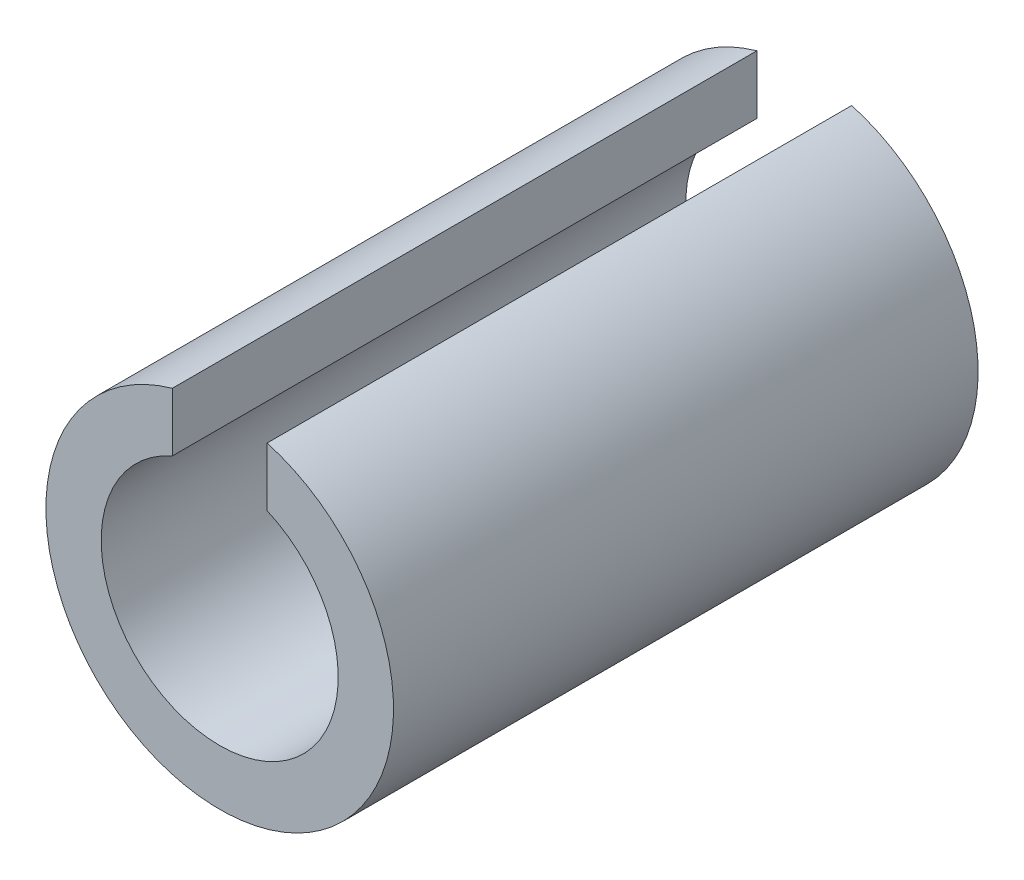
SolidWorks part; units mm, degrees
material "AISI 1020"
ref_plane "Спереди" through (0, 0, 0) normal (0, 0, 1) x (1, 0, 0)
ref_plane "Сверху" through (0, 0, 0) normal (0, 1, 0) x (1, 0, 0)
ref_plane "Справа" through (0, 0, 0) normal (1, 0, 0) x (0, 0, -1)
sketch "Эскиз1" plane through (0, 0, 0) normal (0, 0, 1) x (1, 0, 0)
  line L0 (3, 4.5) -> (3, 6.8739) construction
  line L2 (-3, 6.8739) -> (-3, 10.583)
  line L4 (3, 6.8739) -> (3, 10.583)
  line L5 (-3, 4.5) -> (-3, 6.8739) construction
  line L7 (2.338, -8.662) -> (-2.338, -8.662) construction
  line L8 (2.338, -8.662) -> (2.338, -13.338) construction
  line L9 (2.338, -13.338) -> (-2.338, -13.338) construction
  line L10 (-2.338, -8.662) -> (-2.338, -13.338) construction
  line L11 (2.338, -11) -> (-2.338, -11) construction
  arc A0 (-3, 10.583) -> (3, 10.583) centre (0, 0) ccw
  arc A1 (-3, 6.8739) -> (3, 6.8739) centre (0, 0) ccw
  arc A2 (-3, 6.8739) -> (3, 6.8739) centre (0, 0) ccw construction
  point P21 (0, -8.662)
  dimension "D1" = 22
extrude "Бобышка-Вытянуть1" add sketch "Эскиз1" against normal offset from surface (37 mm away) 56
ref_plane "Плоскость1" through (0, -11, 0) normal (0, -1, 0) x (-1, 0, 0)
sketch "Эскиз2" plane through (0, -11, 0) normal (0, -1, 0) x (-1, 0, 0)
  line L0 (0, 31) -> (0, 6) construction
  line L1 (0, 26) -> (0, -74) construction
  line L2 (3, 31) -> (3, 6)
  line L3 (-3, 31) -> (-3, 6)
  line L4 (11, 37) -> (-11, 37) construction
  line L5 (-11, 0) -> (11, 0) construction
  arc A0 (3, 31) -> (-3, 31) centre (0, 31) ccw
  arc A1 (-3, 6) -> (3, 6) centre (0, 6) ccw
  point P5 (0, 18.5)
  dimension "D1" = 6
  dimension "D2" = 3
  dimension "D3" = 3
extrude "Вырез-Вытянуть1" cut sketch "Эскиз2" against normal blind 3
